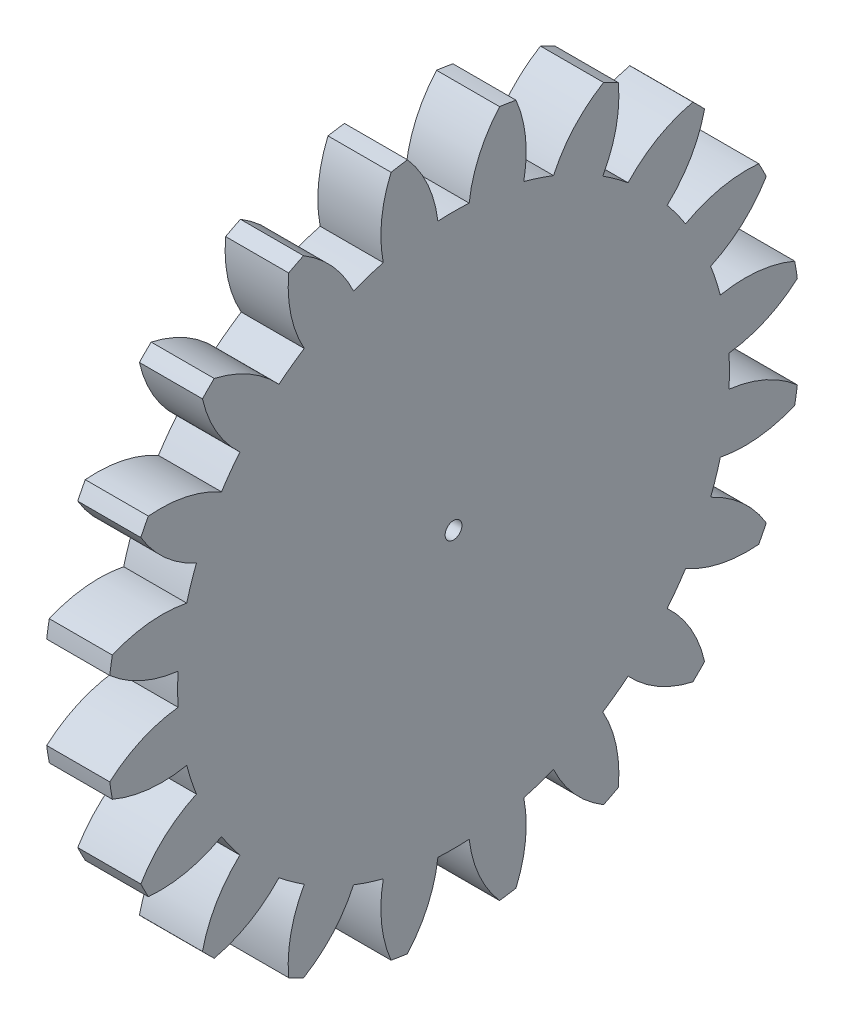
SolidWorks part; units mm, degrees
ref_plane "Plane1" through (0, 0, 0) normal (0, 0, 1) x (1, 0, 0)
ref_plane "Plane2" through (0, 0, 0) normal (0, 1, 0) x (1, 0, 0)
ref_plane "Plane3" through (0, 0, 0) normal (1, 0, 0) x (0, 0, -1)
sketch "HoldingSke" plane through (0, 0, 0) normal (0, 1, 0) x (1, 0, 0)
  line L0 (0, 0) -> (0.6265, -0.228)
  line L1 (-15, 0) -> (100, 0) construction
  line L2 (0, 0) -> (-2.1039, 2.3779)
  line L3 (0, 0) -> (-11.863, 4.5341)
  line L4 (0, 0) -> (8.1152, 2.9537)
  line L5 (0, 0) -> (-46.8476, -17.4728)
  line L6 (0, 0) -> (-2.4869, -1.6779)
  line L7 (-2.1039, 2.3779) -> (8.6586, 51.2059)
  line L8 (-76.2, 54.61) -> (-76.1, 54.61)
  line L9 (-71.009, 38.7566) -> (-53.1078, 45.2721)
  line L10 (-76.2, 71.12) -> (104.1128, 71.12)
  line L11 (0, 0) -> (-3, 0)
  line L12 (-76.2, 101.6) -> (-76.147, 101.6)
  line L13 (24.9733, 27.94) -> (52.9518, 28.4284)
  line L14 (24.9733, 27.94) -> (24.9743, 27.94)
  line L15 (24.9733, 27.94) -> (100.4006, 29.5858)
  line L16 (-63.627, -1.5) -> (-12.827, -1.5)
  circle A0 centre (0, 0) radius 0.4
  circle A1 centre (0, 0) radius 13.124
  circle A2 centre (0, 0) radius 37.5
  circle A3 centre (0, 0) radius 0.4
  dimension "MHD" = 26.248
  dimension "Hub_dia" = 75
  dimension "Bore" = 0.8
  dimension "MBD" = 0.8
  dimension "Num_teeth" = 20
  dimension "Pitch" = 0.6667
  dimension "Overall_len" = 50
  dimension "Show_teeth" = 20
  dimension "Thickness" = 3
  dimension "OAL" = 50.0001
  dimension "T_dim" = 0.1
  dimension "Ap" = 20
  dimension "H" = 19.05
  dimension "Pitch_radius" = 180.3128
  dimension "Width" = 3
  dimension "Backlash" = 0.053
  dimension "Addendum_fac" = 1
  dimension "Dedendum_fac" = 1.25
  dimension "Clearance_fac" = 0.25
  dimension "Dedendum_add" = 0.001
  dimension "Module" = 1.5
sketch "BasProSke" plane through (0, 0, 0) normal (0, 1, 0) x (1, 0, 0)
  line L0 (-10, 0) -> (60, 0) construction
  line L1 (0, 0) -> (0, 16.5)
  line L2 (0, 0) -> (3, 0)
  line L3 (3, 0) -> (3, 16.5)
  line L4 (3, 16.5) -> (0, 16.5)
  dimension "Thickness" = 3
  dimension "Diameter" = 33
revolve "Base-Revolve" add sketch "BasProSke" angle 360 about L0
sketch "TooCutSke" plane through (0, 0, 0) normal (1, 0, 0) x (0, 0, -1)
  line L1 (0, 0) -> (0, 107) construction
  line L2 (0, 0) -> (-1.2696, 14.9462) construction
  line L3 (0, 0) -> (-4.6808, 29.5532) construction
  line L4 (-1.2696, 14.9462) -> (-2.3404, 14.7766) construction
  arc A0 (0.7438, 13.1029) -> (-0.7438, 13.1029) centre (0, 0) ccw
  arc A1 (2.21, 16.377) -> (-2.21, 16.377) centre (0, 0) ccw
  circle A2 centre (0, 0) radius 15 construction
  circle A3 centre (0, 0) radius 14.0954 construction
  arc A4 (-0.7438, 13.1029) -> (-2.21, 16.377) centre (-6.7025, 12.3999) ccw
  arc A5 (2.21, 16.377) -> (0.7438, 13.1029) centre (6.7025, 12.3999) ccw
  dimension "Root_dia" = 26.248
  dimension "Overcut_dia" = 33.0508
  dimension "Pitch_dia" = 30
  dimension "Base_dia" = 28.1908
  dimension "Flank_rad" = 6
  dimension "Half_ang" = 9
  dimension "Half_CT" = 1.0841
extrude "ToothCut" cut sketch "TooCutSke" along normal through all
fillet "Breaks" [suppressed] radius 0.03
fillet "RootFillets" [suppressed] radius 0.376
pattern_circular "TeethCuts" count 20 every 18 about axis through (-10, 0, 0) along (1, 0, 0) of "ToothCut", "RootFillets", "Breaks"
sketch "HubNeaOneSke" plane through (0, 0, 0) normal (-1, 0, 0) x (0, 0, 1)
  circle A0 centre (0, 0) radius 13.124
  dimension "Diameter" = 26.248
extrude "HubNearOne" [suppressed] add sketch "HubNeaOneSke" along normal blind 47.0001
sketch "HubNeaBotSke" plane through (0, 0, 0) normal (-1, 0, 0) x (0, 0, 1)
  circle A0 centre (0, 0) radius 13.124
  dimension "Diameter" = 26.248
extrude "HubNearBoth" [suppressed] add sketch "HubNeaBotSke" along normal blind 23.5
ref_plane "FarPln" through (3, 0, 0) normal (1, 0, 0) x (0, 0, -1)
sketch "HubFarSke" plane through (3, 0, 0) normal (1, 0, 0) x (0, 0, -1)
  circle A0 centre (0, 0) radius 13.124
  dimension "Diameter" = 26.248
extrude "HubFar" [suppressed] add sketch "HubFarSke" along normal blind 23.5
sketch "BorSke" plane through (0, 0, 0) normal (1, 0, 0) x (0, 0, -1)
  circle A0 centre (0, 0) radius 0.4
  dimension "Diameter" = 0.8
extrude "Bore" cut sketch "BorSke" along normal mid plane 100.0001
sketch "KeySke" plane through (0, 0, 0) normal (1, 0, 0) x (0, 0, -1)
  line L0 (-0.05, 0) -> (-0.05, 0.5)
  line L1 (-0.05, 0.5) -> (0.05, 0.5)
  line L2 (0.05, 0.5) -> (0.05, 0)
  line L3 (0, 0) -> (0, 34) construction
  line L4 (-0.05, 0) -> (0.05, 0)
  dimension "Offset" = 0.5
  dimension "Width" = 0.1
extrude "Keyway" [suppressed] cut sketch "KeySke" along normal mid plane 100.0001
pattern_circular "Keyway2" [suppressed] count 2 every 90 about axis through (-10, 0, 0) along (1, 0, 0)
equation "' \"Module@HoldingSke\" = 6.35"
equation "' \"Num_teeth@HoldingSke\" = 12"
equation "' \"Ap@HoldingSke\" =  20"
equation "' \"Ap@HoldingSke\" = 20"
equation "' \"Width@HoldingSke\" = 0.5 * 25.4"
equation "' \"Hub_dia@HoldingSke\"= 1 * 25.4"
equation "' \"Hub_dia@HoldingSke\" = 1 * 25.4"
equation "' \"Overall_len@HoldingSke\" = 1.0 * 25.4"
equation "' \"Bore@HoldingSke\" = 0.75 * 25.4"
equation "' \"T_dim@HoldingSke\" = 0.1 * 25.4"
equation "' \"Width@KeySke\" = 0.25 * 25.4"
equation "' \"Show_teeth@HoldingSke\" = 13"
equation "' \"Backlash@HoldingSke\" = 0.009 * 25.4"
equation "' \"Addendum_fac@HoldingSke\" = 1.0"
equation "' \"Dedendum_fac@HoldingSke\" = 1.25"
equation "' \"Dedendum_add@HoldingSke\" = 0.00005 * 25.4"
equation "' \"Clearance_fac@HoldingSke\" = 0.25"
equation "\"Pitch@HoldingSke\" = 1 / \"Module@HoldingSke\""
equation "\"Overcut_dia@TooCutSke\" = (\"Num_teeth@HoldingSke\" + 2 * \"Addendum_fac@HoldingSke\") / \"Pitch@HoldingSke\" + 0.002 * 25.4"
equation "\"Pitch_dia@TooCutSke\" = \"Num_teeth@HoldingSke\" / \"Pitch@HoldingSke\""
equation "\"Base_dia@TooCutSke\" = \"Num_teeth@HoldingSke\" / \"Pitch@HoldingSke\" * cos((\"Ap@HoldingSke\"  * 3.14159265 / 180))"
equation "\"Root_dia@TooCutSke\" = (\"Num_teeth@HoldingSke\" + 2) / \"Pitch@HoldingSke\" - 2 * (\"Addendum_fac@HoldingSke\" + \"Dedendum_fac@HoldingSke\") / \"Pitch@HoldingSke\" - \"Dedendum_add@HoldingSke\" * 2"
equation "\"Half_ang@TooCutSke\" = 180 / \"Num_teeth@HoldingSke\""
equation "\"Half_CT@TooCutSke\" = \"Num_teeth@HoldingSke\" / \"Pitch@HoldingSke\" * sin((3.14159265 / 2 / \"Num_teeth@HoldingSke\")) / 2 - 7 * \"Backlash@HoldingSke\" / 4"
equation "\"Flank_rad@TooCutSke\" = \"Num_teeth@HoldingSke\" / \"Pitch@HoldingSke\" / 5"
equation "\"Radius@RootFillets\" = \"Clearance_fac@HoldingSke\" / \"Pitch@HoldingSke\" + \"Dedendum_add@HoldingSke\""
equation "\"Break_rad@Breaks\" = 0.02 / \"Pitch@HoldingSke\""
equation "\"Thickness@HoldingSke\" = \"Width@HoldingSke\""
equation "\"OAL@HoldingSke\" = \"Thickness@HoldingSke\""
equation "\"MHD@HoldingSke\" = (\"Num_teeth@HoldingSke\" + 2) / \"Pitch@HoldingSke\" - 2 * (\"Addendum_fac@HoldingSke\" + \"Dedendum_fac@HoldingSke\")  / \"Pitch@HoldingSke\" - \"Dedendum_add@HoldingSke\" * 2"
equation "\"MBD@HoldingSke\" = (\"Num_teeth@HoldingSke\" + 2) / \"Pitch@HoldingSke\" - 2 * (\"Addendum_fac@HoldingSke\" + \"Dedendum_fac@HoldingSke\")  / \"Pitch@HoldingSke\" - \"Dedendum_add@HoldingSke\" * 2 - 0.002 * 25.4"
equation "\"MHD@HoldingSke\" = ((sgn( \"MHD@HoldingSke\" - \"Hub_dia@HoldingSke\" )-1)*( \"MHD@HoldingSke\" - \"Hub_dia@HoldingSke\" ))/-2+ \"Hub_dia@HoldingSke\""
equation "\"MBD@HoldingSke\" = ((sgn( \"MBD@HoldingSke\" - \"Bore@HoldingSke\" )-1)*( \"MBD@HoldingSke\" - \"Bore@HoldingSke\" ))/-2+ \"Bore@HoldingSke\""
equation "\"OAL@HoldingSke\" = ((sgn( \"OAL@HoldingSke\" - \"Overall_len@HoldingSke\" )+1)*( \"OAL@HoldingSke\" - \"Overall_len@HoldingSke\" ))/2 + \"Overall_len@HoldingSke\" + 0.000002 * 25.4"
equation "\"Num_teeth@TeethCuts\" = int( \"Show_teeth@HoldingSke\" ) + 1"
equation "\"Num_teeth@TeethCuts\" = ((sgn( \"Num_teeth@TeethCuts\" - \"Num_teeth@HoldingSke\" )-1)*( \"Num_teeth@TeethCuts\" - \"Num_teeth@HoldingSke\" ))/-2+ \"Num_teeth@HoldingSke\""
equation "\"Num_teeth@TeethCuts\" = ((sgn( \"Num_teeth@TeethCuts\" - 2.0)+1)*( \"Num_teeth@TeethCuts\" - 2.0))/2 +2.0"
equation "\"Angle@TeethCuts\" = 360.0 / \"Num_teeth@HoldingSke\""
equation "\"Diameter@BasProSke\" = (\"Num_teeth@HoldingSke\" + 2 * \"Addendum_fac@HoldingSke\") / \"Pitch@HoldingSke\""
equation "\"Thickness@BasProSke\"  = \"Thickness@HoldingSke\""
equation "' \"Fillet_rad@BasProSke\" =  \"Thickness@HoldingSke\" * 0.05"
equation "' \"Fillet_rad@BasProSke\" = \"Thickness@HoldingSke\" * 0.05"
equation "\"MHD@HoldingSke\" = ((sgn( \"MHD@HoldingSke\" - \"Root_dia@TooCutSke\" )-1)*( \"MHD@HoldingSke\" - \"Root_dia@TooCutSke\" ))/-2+ \"Root_dia@TooCutSke\""
equation "\"Diameter@HubNeaOneSke\" = \"MHD@HoldingSke\""
equation "\"Length@HubNearOne\" = \"OAL@HoldingSke\" - \"Thickness@BasProSke\""
equation "\"Diameter@HubNeaBotSke\" = \"MHD@HoldingSke\""
equation "\"Length@HubNearBoth\" = ( \"OAL@HoldingSke\" - \"Thickness@BasProSke\" ) / 2.0"
equation "\"Thickness@FarPln\" = \"Thickness@BasProSke\""
equation "\"Diameter@HubFarSke\" = \"MHD@HoldingSke\""
equation "\"Length@HubFar\" = ( \"OAL@HoldingSke\" - \"Thickness@BasProSke\" ) / 2.0"
equation "\"Diameter@BorSke\" = \"MBD@HoldingSke\""
equation "\"D1@Bore\" = \"OAL@HoldingSke\" * 2.0"
equation "\"D1@Keyway\" = \"OAL@HoldingSke\" * 2.0"
equation "\"Offset@KeySke\" = \"T_dim@HoldingSke\" + \"MBD@HoldingSke\" / 2.0"
